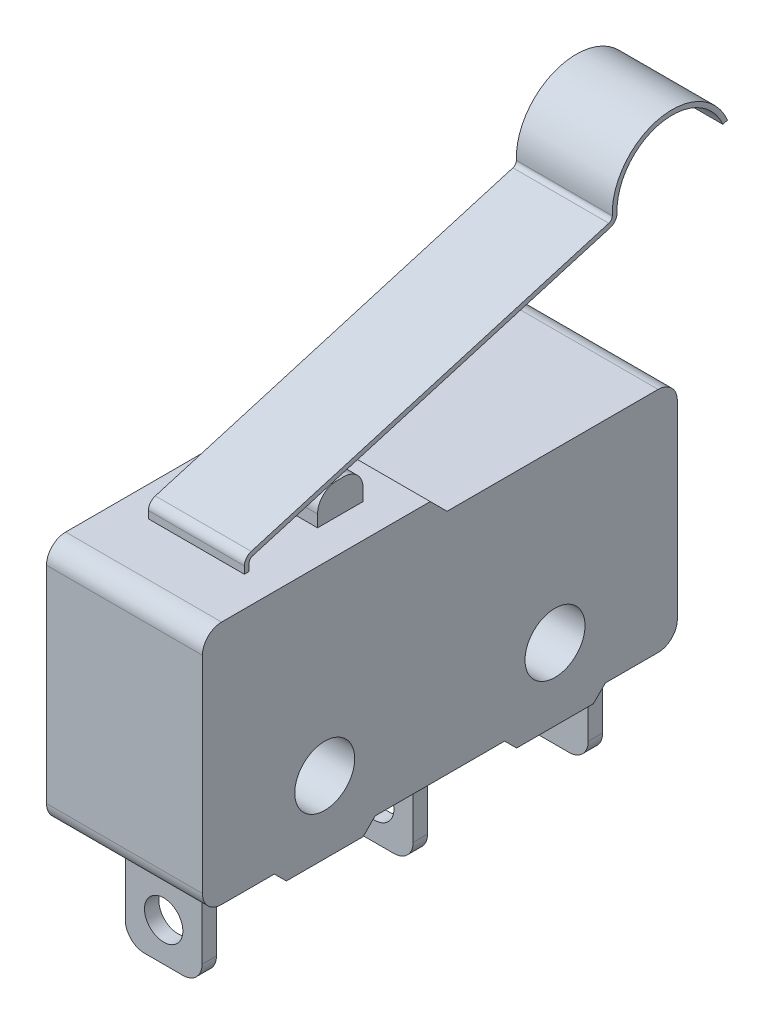
SolidWorks part; units mm, degrees
ref_plane "Спереди" through (0, 0, 0) normal (0, 0, 1) x (1, 0, 0)
ref_plane "Сверху" through (0, 0, 0) normal (0, 1, 0) x (1, 0, 0)
ref_plane "Справа" through (0, 0, 0) normal (1, 0, 0) x (0, 0, -1)
sketch "Эскиз1" plane through (0, 0, 0) normal (1, 0, 0) x (0, 0, -1)
  line L0 (-9.9, 5.1) -> (-9.9, -5.1)
  line L1 (-9.9, -5.1) -> (-6.9, -5.1)
  line L2 (-6.9, -5.1) -> (-6.4, -5.6)
  line L3 (-6.4, -5.6) -> (-3.2, -5.6)
  line L4 (-3.2, -5.6) -> (-2.7, -5.1)
  line L5 (-2.7, -5.1) -> (2.7, -5.1)
  line L6 (2.7, -5.1) -> (3.2, -5.6)
  line L7 (3.2, -5.6) -> (6.4, -5.6)
  line L8 (6.4, -5.6) -> (6.9, -5.1)
  line L9 (6.9, -5.1) -> (9.9, -5.1)
  line L10 (9.9, -5.1) -> (9.9, 4.4)
  line L11 (9.9, 4.4) -> (0.3, 4.4)
  line L12 (0.3, 4.4) -> (-0.4, 5.1)
  line L13 (-0.4, 5.1) -> (-9.9, 5.1)
  line L14 (-9.9, 0) -> (9.9, 0) construction
  line L15 (-4.8, -5.6) -> (-4.8, 0) construction
  line L16 (4.8, -5.6) -> (4.8, 0) construction
  circle A0 centre (-4.8, -2.6) radius 1.25
  circle A1 centre (4.8, -2.6) radius 1.25
  dimension "D10" = 2.5
  dimension "D1" = 19.8
  dimension "D2" = 10.2
  dimension "D3" = 9.5
  dimension "D4" = 45
  dimension "D5" = 3.2
  dimension "D6" = 5.4
  dimension "D7" = 9.6
  dimension "D8" = 10
  dimension "D9" = 3
extrude "Бобышка-Вытянуть1" add sketch "Эскиз1" along normal mid plane 6.5
sketch "Эскиз4" plane through (0, 0, 0) normal (1, 0, 0) x (0, 0, -1)
  line L0 (-9.9, -5.1) -> (-6.9, -5.1) construction
  line L1 (0.5349, -5.1) -> (0.5349, -9.3)
  line L2 (-8.2651, -5.1) -> (-8.2651, -9.3)
  line L3 (-8.2651, -9.3) -> (-7.6651, -9.3)
  line L4 (-7.6651, -5.1) -> (-7.6651, -9.3)
  line L7 (-8.2651, -5.1) -> (-7.6651, -5.1)
  line L8 (0.5349, -9.3) -> (1.1349, -9.3)
  line L9 (1.1349, -5.1) -> (1.1349, -9.3)
  line L12 (0.5349, -5.1) -> (1.1349, -5.1)
  line L13 (7.8349, -5.1) -> (7.8349, -9.3)
  line L14 (7.8349, -9.3) -> (8.4349, -9.3)
  line L15 (8.4349, -5.1) -> (8.4349, -9.3)
  line L18 (7.8349, -5.1) -> (8.4349, -5.1)
  dimension "D1" = 4.2
  dimension "D2" = 0.6
  dimension "D3" = 8.8
  dimension "D4" = 7.3
extrude "Бобышка-Вытянуть4" add sketch "Эскиз4" along normal mid plane 3.2
fillet "Скругление1" radius 0.8 10 edges at (0, -5.1, -9.9) (0, 4.4, -9.9) (0, -5.1, 9.9) (0, 5.1, 9.9) (-1.6, -9.3, -8.1349) (1.6, -9.3, -8.1349) (-1.6, -9.3, 7.9651) (-1.6, -9.3, -0.8349) (1.6, -9.3, -0.8349) (1.6, -9.3, 7.9651)
sketch "Эскиз2" plane through (0, 5.1, 0) normal (0, 1, 0) x (1, 0, 0)
  line L0 (0, -0.4) -> (0, -9.9) construction
  line L1 (-1.85, -1.8) -> (1.85, -1.8)
  line L2 (-1.85, -1.8) -> (-1.85, -3.7)
  line L3 (-1.85, -3.7) -> (1.85, -3.7)
  line L4 (1.85, -1.8) -> (1.85, -3.7)
  line L5 (-1.85, -1.8) -> (1.85, -3.7) construction
  line L6 (-1.85, -3.7) -> (1.85, -1.8) construction
  line L7 (3.25, -0.4) -> (-3.25, -0.4) construction
  line L8 (3.25, -9.9) -> (-3.25, -9.9) construction
  point P0 (0, -2.75)
  dimension "D1" = 3.7
  dimension "D2" = 1.9
  dimension "D3" = 6.2
extrude "Бобышка-Вытянуть2" add sketch "Эскиз2" along normal blind 1.3
fillet "Скругление2" radius 0.8 2 edges at (0, 6.4, 1.8) (0, 6.4, 3.7)
sketch "Эскиз3" plane through (0, 0, 0) normal (1, 0, 0) x (0, 0, -1)
  line L0 (-6.9, 5.1) -> (-6.9, 5.7)
  line L1 (-0.4, 5.1) -> (-9.1, 5.1) construction
  line L2 (-6.9, 5.7) -> (8.4475, 10.2225)
  line L3 (-9.9, 4.3) -> (-9.9, -4.3) construction
  line L4 (13.0488, 11.3698) -> (13.2419, 11.4267)
  line L5 (-6.7, 5.1) -> (-6.7, 5.5504)
  line L6 (-6.7, 5.5504) -> (8.6681, 10.0789)
  line L7 (8.6681, 10.0789) -> (13.0488, 11.3698) construction
  line L8 (-6.9, 5.1) -> (-6.7, 5.1)
  arc A0 (8.4475, 10.2225) -> (13.2419, 11.4267) centre (10.9362, 10.4605) cw
  arc A1 (8.6681, 10.0789) -> (13.0488, 11.3698) centre (10.9362, 10.4605) cw
  arc A2 (8.6681, 10.0789) -> (13.0575, 11.3494) centre (10.9362, 10.4605) cw construction
  dimension "D4" = 2.5
  dimension "D1" = 3
  dimension "D2" = 0.6
  dimension "D3" = 16
  dimension "D5" = 0.2
extrude "Бобышка-Вытянуть3" add sketch "Эскиз3" along normal mid plane 4
fillet "Скругление4" radius 0.2 2 edges at (0, 5.5504, 6.7) (0, 10.2225, -8.4475)
fillet "Скругление3" radius 0.4 2 edges at (0, 5.7, 6.9) (0, 10.0789, -8.6681)
sketch "Эскиз5" plane through (0, 0, 8.2651) normal (0, 0, 1) x (1, 0, 0)
  line L0 (0.8, -9.3) -> (-0.8, -9.3) construction
  circle A0 centre (0, -7.7) radius 0.8
  point P2 (0, -9.3)
  dimension "D1" = 1.6
  dimension "D2" = 1.6
extrude "Вырез-Вытянуть1" cut sketch "Эскиз5" against normal up to surface (16.7 mm away) up to face at (0, -7.6886, -8.4349)
